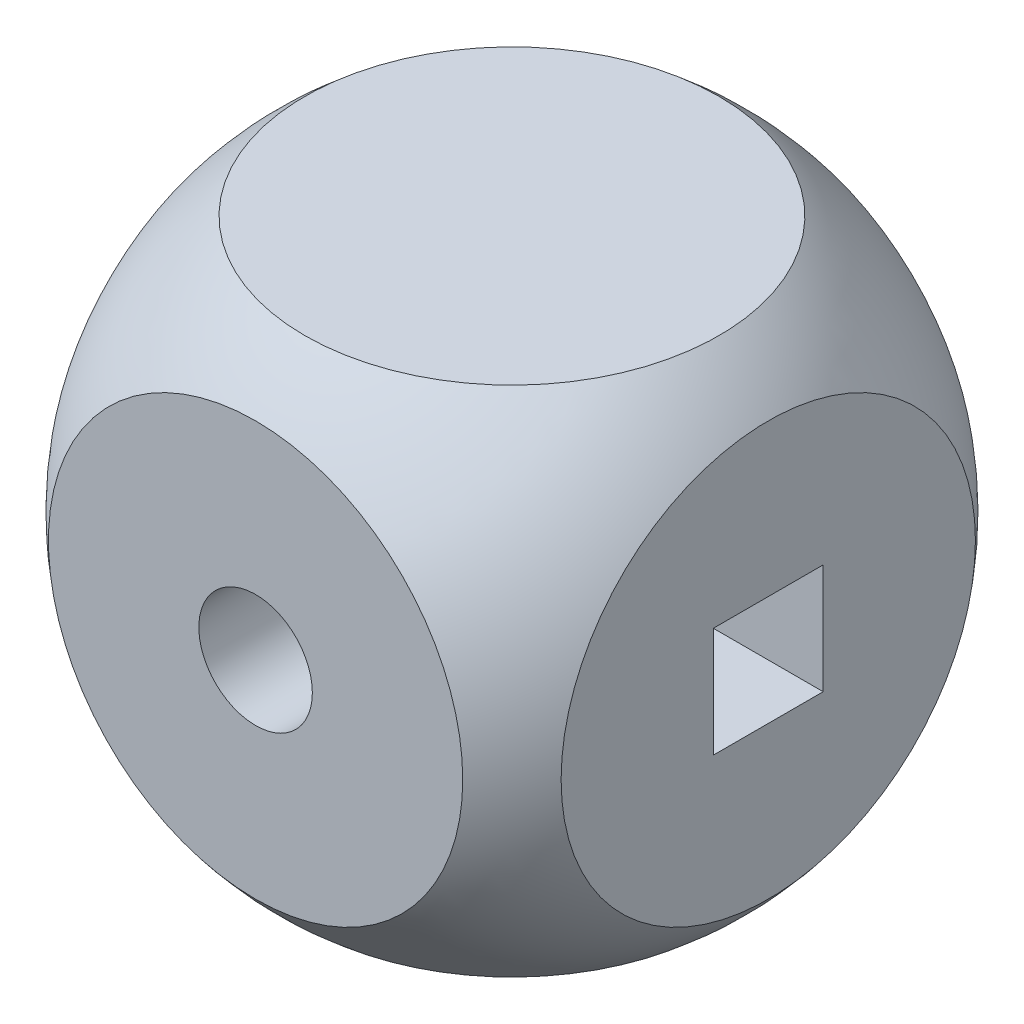
SolidWorks part; units mm, degrees
material "6061 합금"
ref_plane "정면" through (0, 0, 0) normal (0, 0, 1) x (1, 0, 0)
ref_plane "윗면" through (0, 0, 0) normal (0, 1, 0) x (1, 0, 0)
ref_plane "우측면" through (0, 0, 0) normal (1, 0, 0) x (0, 0, -1)
sketch "스케치1" plane through (0, 0, 0) normal (0, 0, 1) x (1, 0, 0)
  line L0 (0, 0.8636) -> (0, -0.67) construction
  line L1 (0, 9) -> (0, -9)
  arc A0 (0, -9) -> (0, 9) centre (0, 0) ccw
  dimension "D1" = 18
revolve "회전42" add sketch "스케치1" angle 360 about L1
ref_plane "평면1" through (0, 0, 9) normal (0, 0, 1) x (1, 0, 0)
ref_plane "평면2" through (0, 9, 0) normal (0, 1, 0) x (1, 0, 0)
ref_plane "평면3" through (9, 0, 0) normal (1, 0, 0) x (0, 0, -1)
sketch "스케치6" plane through (0, 0, 9) normal (0, 0, 1) x (1, 0, 0)
  circle A0 centre (0, 0) radius 10
  dimension "D1" = 20
extrude "컷-돌출4" cut sketch "스케치6" against normal blind 2
mirror "대칭 복사4" about plane through (0, 0, 0) normal (0, 0, 1) of "컷-돌출4"
sketch "스케치7" plane through (0, 9, 0) normal (0, 1, 0) x (1, 0, 0)
  circle A0 centre (0, 0) radius 10
  dimension "D1" = 20
extrude "컷-돌출5" cut sketch "스케치7" against normal blind 2
mirror "대칭 복사5" about plane through (0, 0, 0) normal (0, 1, 0) of "컷-돌출5"
sketch "스케치8" plane through (9, 0, 0) normal (1, 0, 0) x (0, 0, -1)
  circle A0 centre (0, 0) radius 10
  dimension "D1" = 20
extrude "컷-돌출6" cut sketch "스케치8" against normal blind 2
mirror "대칭 복사6" about plane through (0, 0, 0) normal (1, 0, 0) of "컷-돌출6"
sketch "스케치9" plane through (0, 0, 7) normal (0, 0, 1) x (1, 0, 0)
  circle A0 centre (0, 0) radius 1.55
  dimension "D1" = 3.1
extrude "컷-돌출7" cut sketch "스케치9" against normal through all
sketch "스케치10" plane through (0, 7, 0) normal (0, 1, 0) x (1, 0, 0)
  circle A0 centre (0, 0) radius 1.55
  dimension "D1" = 3.1
sketch "스케치11" plane through (7, 0, 0) normal (1, 0, 0) x (0, 0, -1)
  line L1 (-1.5, 1.5) -> (1.5, 1.5)
  line L2 (-1.5, 1.5) -> (-1.5, -1.5)
  line L3 (-1.5, -1.5) -> (1.5, -1.5)
  line L4 (1.5, 1.5) -> (1.5, -1.5)
  line L5 (-1.5, 1.5) -> (1.5, -1.5) construction
  line L6 (-1.5, -1.5) -> (1.5, 1.5) construction
  dimension "D1" = 3
  dimension "D2" = 3
extrude "컷-돌출9" cut sketch "스케치11" against normal through all
sketch "스케치12" plane through (0, 0, 0) normal (0, 0, 1) x (1, 0, 0)
  circle A0 centre (0, 0) radius 9 construction
  circle A1 centre (0, 0) radius 9.25 construction
  circle A2 centre (0, 0) radius 12 construction
  dimension "D1" = 18
  dimension "D2" = 18.5
  dimension "D3" = 24
sketch "스케치13" plane through (0, 0, 7) normal (0, 0, 1) x (1, 0, 0)
  circle A0 centre (0, 0) radius 5.6569 construction
sketch "스케치14" plane through (0, 0, -7) normal (0, 0, -1) x (-1, 0, 0)
  circle A0 centre (0, 0) radius 5.6569 construction
